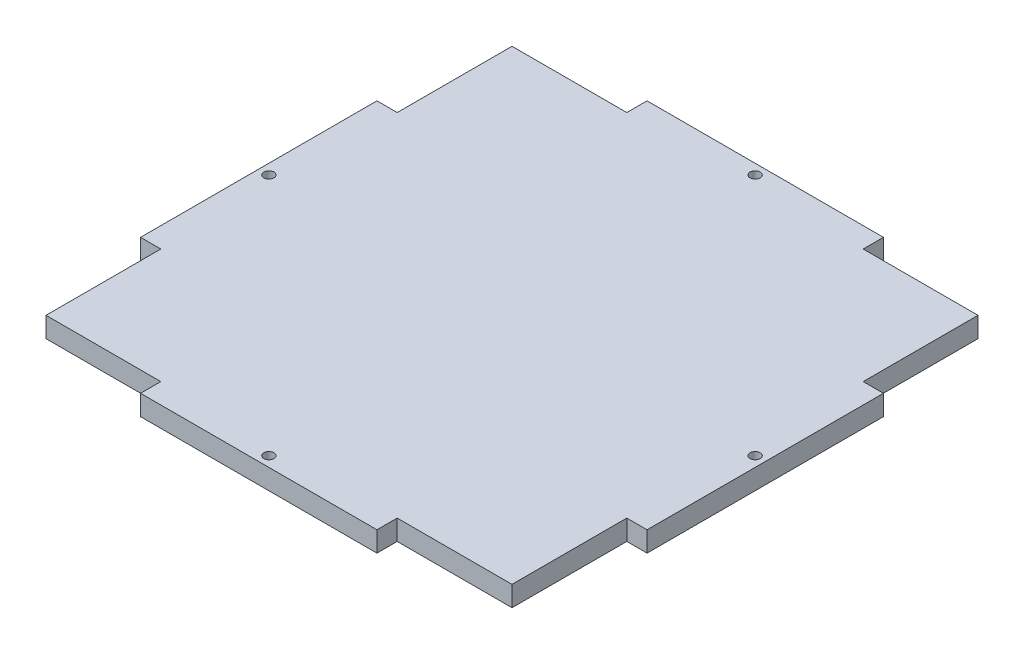
SolidWorks part; units mm, degrees
ref_plane "Front Plane" through (0, 0, 0) normal (0, 0, 1) x (1, 0, 0)
ref_plane "Top Plane" through (0, 0, 0) normal (0, 1, 0) x (1, 0, 0)
ref_plane "Right Plane" through (0, 0, 0) normal (1, 0, 0) x (0, 0, -1)
sketch "Sketch1" plane through (0, 0, 0) normal (0, 1, 0) x (1, 0, 0)
  line L0 (-35, 69) -> (-75, 69)
  line L1 (-75, -75) -> (75, -75)
  line L2 (-75, -75) -> (-75, 75)
  line L3 (-75, 75) -> (75, 75)
  line L4 (75, -75) -> (75, 75)
  line L5 (-75, -75) -> (75, 75) construction
  line L6 (-75, 75) -> (75, -75) construction
  line L7 (-35, 75) -> (35, 75)
  line L8 (-35, 75) -> (-35, 69)
  line L9 (-35, 69) -> (35, 69)
  line L10 (35, 75) -> (35, 69)
  line L11 (-75, 69) -> (75, 69)
  line L12 (-69, 75) -> (-69, -75)
  line L13 (-69, 35) -> (-69, -35)
  line L14 (-75, -35) -> (-69, -35)
  line L15 (-75, 35) -> (-75, -35)
  line L16 (-75, 35) -> (-69, 35)
  line L17 (69, -75) -> (69, 75)
  line L18 (69, -35) -> (69, 35)
  line L19 (75, 35) -> (69, 35)
  line L20 (75, -35) -> (75, 35)
  line L21 (75, -35) -> (69, -35)
  line L22 (-107.7873, 0) -> (120.731, 0) construction
  line L23 (-75, -69) -> (75, -69)
  line L24 (-35, -69) -> (-75, -69)
  line L25 (-35, -69) -> (35, -69)
  line L26 (35, -75) -> (35, -69)
  line L27 (-35, -75) -> (35, -75)
  line L28 (-35, -75) -> (-35, -69)
  line L29 (0, 92.4735) -> (0, -90.0598) construction
  circle A0 centre (0, 72) radius 1.5
  circle A1 centre (-72, 0) radius 1.5
  circle A2 centre (72, 0) radius 1.5
  circle A3 centre (0, -72) radius 1.5
  point P0 (0, 0)
  dimension "D6" = 3
  dimension "D1" = 150
  dimension "D2" = 150
  dimension "D3" = 6
  dimension "D4" = 40
  dimension "D5" = 40
  dimension "D7" = 3
extrude "Boss-Extrude1" add sketch "Sketch1" along normal blind 6 contours L12 L23 L17 L11 L9 L0 | L10 L3 L8 L9 | L21 L4 L19 L17 | L28 L1 L26 L23 | L16 L2 L14 L12
